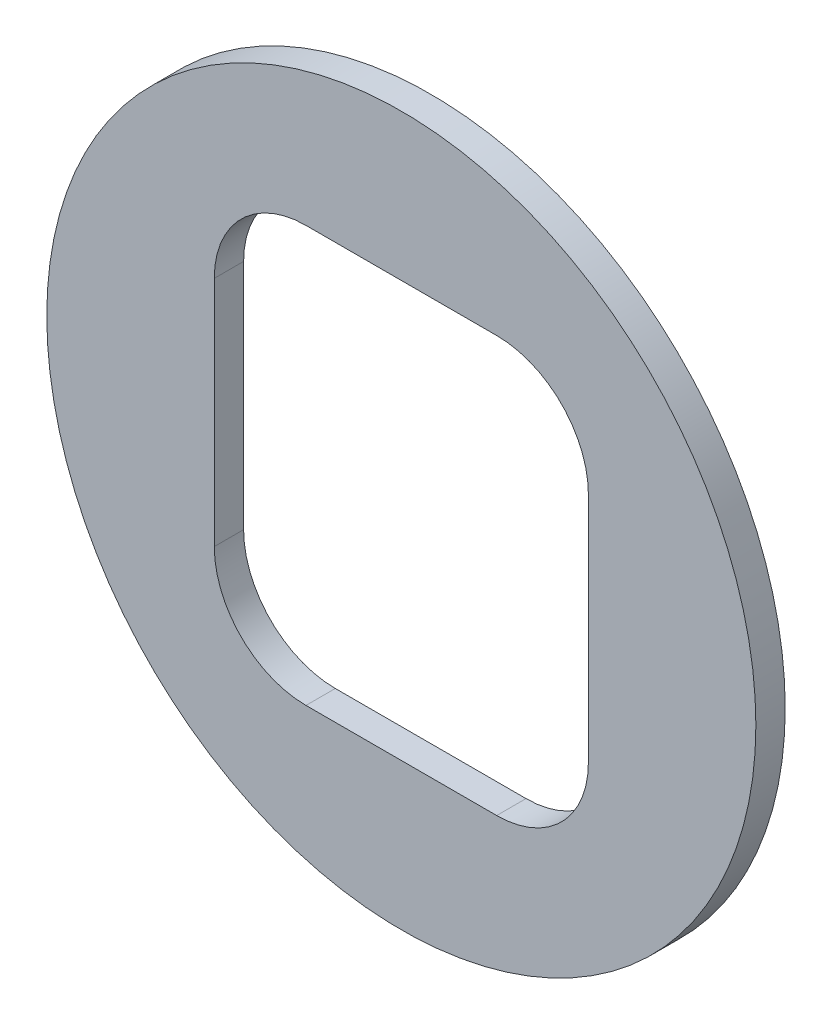
SolidWorks part; units mm, degrees
material "304, 316 OR 302 SSTL"
ref_plane "XY" through (0, 0, 0) normal (0, 0, 1) x (1, 0, 0)
ref_plane "XZ" through (0, 0, 0) normal (0, 1, 0) x (1, 0, 0)
ref_plane "YZ" through (0, 0, 0) normal (1, 0, 0) x (0, 0, -1)
sketch "Sketch1" plane through (0, 0, 0) normal (0, 0, 1) x (1, 0, 0)
  line L0 (-9.7155, 10.795) -> (9.7155, -10.795) construction
  line L1 (-9.7155, 10.795) -> (9.7155, 10.795)
  line L2 (-9.7155, 10.795) -> (-9.7155, -10.795)
  line L3 (-9.7155, -10.795) -> (9.7155, -10.795)
  line L4 (9.7155, 10.795) -> (9.7155, -10.795)
  circle A0 centre (0, 0) radius 18.415
  dimension "D1" = 36.83
  dimension "D2" = 19.431
  dimension "D3" = 21.59
extrude "Extrude1" add sketch "Sketch1" along normal blind 1.524
fillet "Fillet1" radius 4.7625 4 edges at (-9.7155, -10.795, 0.762) (9.7155, -10.795, 0.762) (9.7155, 10.795, 0.762) (-9.7155, 10.795, 0.762)
